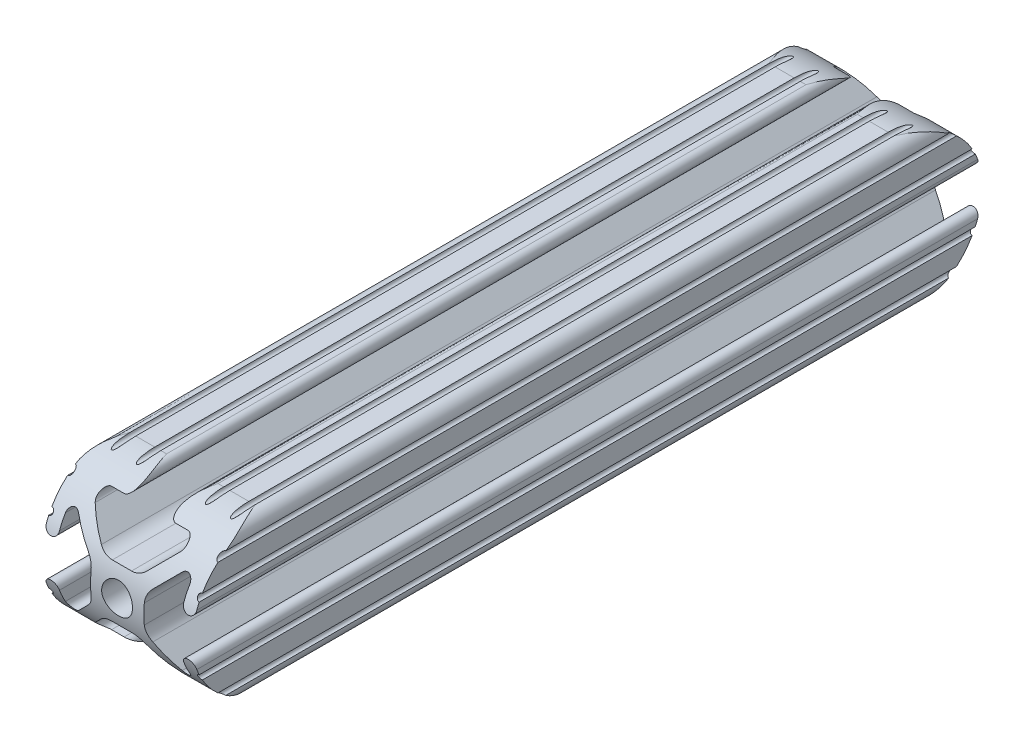
SolidWorks part; units mm, degrees
ref_plane "Front Plane" through (0, 0, 0) normal (0, 0, 1) x (1, 0, 0)
ref_plane "Top Plane" through (0, 0, 0) normal (0, 1, 0) x (1, 0, 0)
ref_plane "Right Plane" through (0, 0, 0) normal (1, 0, 0) x (0, 0, -1)
ref_plane "Plane1" through (0, 0, -450.85) normal (0, 0, -1) x (-1, 0, 0)
sketch "Sketch1" plane through (0, 0, -450.85) normal (0, 0, -1) x (-1, 0, 0)
  line L0 (12.7, -9.5504) -> (12.7, -6.3331)
  line L1 (12.7, -5.3171) -> (12.7, -4.3434)
  line L2 (10.4902, -4.3434) -> (10.4902, -6.4748)
  line L3 (8.7558, -7.1932) -> (5.4257, -3.8632)
  line L4 (4.4958, -1.6181) -> (4.4958, 1.6181)
  line L5 (5.4257, 3.8632) -> (8.7558, 7.1932)
  line L6 (10.4902, 6.4748) -> (10.4902, 4.3434)
  line L7 (12.7, 4.3434) -> (12.7, 5.3171)
  line L8 (12.7, 6.3331) -> (12.7, 9.5504)
  line L9 (9.5504, 12.7) -> (6.3331, 12.7)
  line L10 (5.3171, 12.7) -> (4.3434, 12.7)
  line L11 (4.3434, 10.4902) -> (6.4748, 10.4902)
  line L12 (7.1932, 8.7558) -> (3.8632, 5.4257)
  line L13 (1.6181, 4.4958) -> (-1.6181, 4.4958)
  line L14 (-3.8632, 5.4257) -> (-7.1932, 8.7558)
  line L15 (-6.4748, 10.4902) -> (-4.3434, 10.4902)
  line L16 (-4.3434, 12.7) -> (-5.3171, 12.7)
  line L17 (-6.3331, 12.7) -> (-9.5504, 12.7)
  line L18 (-12.7, 9.5504) -> (-12.7, 6.3331)
  line L19 (-12.7, 5.3171) -> (-12.7, 4.3434)
  line L20 (-10.4902, 4.3434) -> (-10.4902, 6.4748)
  line L21 (-8.7558, 7.1932) -> (-5.4257, 3.8632)
  line L22 (-4.4958, 1.6181) -> (-4.4958, -1.6181)
  line L23 (-5.4257, -3.8632) -> (-8.7558, -7.1932)
  line L24 (-10.4902, -6.4748) -> (-10.4902, -4.3434)
  line L25 (-12.7, -4.3434) -> (-12.7, -5.3171)
  line L26 (-12.7, -6.3331) -> (-12.7, -9.5504)
  line L27 (-9.5504, -12.7) -> (-6.3331, -12.7)
  line L28 (-5.3171, -12.7) -> (-4.3434, -12.7)
  line L29 (-4.3434, -10.4902) -> (-6.4748, -10.4902)
  line L30 (-7.1932, -8.7558) -> (-3.8632, -5.4257)
  line L31 (-1.6181, -4.4958) -> (1.6181, -4.4958)
  line L32 (3.8632, -5.4257) -> (7.1932, -8.7558)
  line L33 (6.4748, -10.4902) -> (4.3434, -10.4902)
  line L34 (4.3434, -12.7) -> (5.3171, -12.7)
  line L35 (6.3331, -12.7) -> (9.5504, -12.7)
  arc A0 (12.6998, -10.5664) -> (12.7, -9.5504) centre (12.7, -10.0584) cw
  arc A1 (12.7, -6.3331) -> (12.7, -5.3171) centre (12.7, -5.8251) cw
  arc A2 (12.7, -4.3434) -> (10.4902, -4.3434) centre (11.5951, -4.3434) ccw
  arc A3 (10.4902, -6.4748) -> (8.7558, -7.1932) centre (9.4742, -6.4748) cw
  arc A4 (5.4257, -3.8632) -> (4.4958, -1.6181) centre (7.6708, -1.6181) cw
  arc A5 (4.4958, 1.6181) -> (5.4257, 3.8632) centre (7.6708, 1.6181) cw
  arc A6 (8.7558, 7.1932) -> (10.4902, 6.4748) centre (9.4742, 6.4748) cw
  arc A7 (10.4902, 4.3434) -> (12.7, 4.3434) centre (11.5951, 4.3434) ccw
  arc A8 (12.7, 5.3171) -> (12.7, 6.3331) centre (12.7, 5.8251) cw
  arc A9 (12.7, 9.5504) -> (12.6998, 10.5664) centre (12.7, 10.0584) cw
  arc A10 (12.6998, 10.5664) -> (10.5664, 12.6998) centre (10.5918, 10.5918) ccw
  arc A11 (10.5664, 12.6998) -> (9.5504, 12.7) centre (10.0584, 12.7) cw
  arc A12 (6.3331, 12.7) -> (5.3171, 12.7) centre (5.8251, 12.7) cw
  arc A13 (4.3434, 12.7) -> (4.3434, 10.4902) centre (4.3434, 11.5951) ccw
  arc A14 (6.4748, 10.4902) -> (7.1932, 8.7558) centre (6.4748, 9.4742) cw
  arc A15 (3.8632, 5.4257) -> (1.6181, 4.4958) centre (1.6181, 7.6708) cw
  arc A16 (-1.6181, 4.4958) -> (-3.8632, 5.4257) centre (-1.6181, 7.6708) cw
  arc A17 (-7.1932, 8.7558) -> (-6.4748, 10.4902) centre (-6.4748, 9.4742) cw
  arc A18 (-4.3434, 10.4902) -> (-4.3434, 12.7) centre (-4.3434, 11.5951) ccw
  arc A19 (-5.3171, 12.7) -> (-6.3331, 12.7) centre (-5.8251, 12.7) cw
  arc A20 (-9.5504, 12.7) -> (-10.5664, 12.6998) centre (-10.0584, 12.7) cw
  arc A21 (-10.5664, 12.6998) -> (-12.6998, 10.5664) centre (-10.5918, 10.5918) ccw
  arc A22 (-12.6998, 10.5664) -> (-12.7, 9.5504) centre (-12.7, 10.0584) cw
  arc A23 (-12.7, 6.3331) -> (-12.7, 5.3171) centre (-12.7, 5.8251) cw
  arc A24 (-12.7, 4.3434) -> (-10.4902, 4.3434) centre (-11.5951, 4.3434) ccw
  arc A25 (-10.4902, 6.4748) -> (-8.7558, 7.1932) centre (-9.4742, 6.4748) cw
  arc A26 (-5.4257, 3.8632) -> (-4.4958, 1.6181) centre (-7.6708, 1.6181) cw
  arc A27 (-4.4958, -1.6181) -> (-5.4257, -3.8632) centre (-7.6708, -1.6181) cw
  arc A28 (-8.7558, -7.1932) -> (-10.4902, -6.4748) centre (-9.4742, -6.4748) cw
  arc A29 (-10.4902, -4.3434) -> (-12.7, -4.3434) centre (-11.5951, -4.3434) ccw
  arc A30 (-12.7, -5.3171) -> (-12.7, -6.3331) centre (-12.7, -5.8251) cw
  arc A31 (-12.7, -9.5504) -> (-12.6998, -10.5664) centre (-12.7, -10.0584) cw
  arc A32 (-12.6998, -10.5664) -> (-10.5664, -12.6998) centre (-10.5918, -10.5918) ccw
  arc A33 (-10.5664, -12.6998) -> (-9.5504, -12.7) centre (-10.0584, -12.7) cw
  arc A34 (-6.3331, -12.7) -> (-5.3171, -12.7) centre (-5.8251, -12.7) cw
  arc A35 (-4.3434, -12.7) -> (-4.3434, -10.4902) centre (-4.3434, -11.5951) ccw
  arc A36 (-6.4748, -10.4902) -> (-7.1932, -8.7558) centre (-6.4748, -9.4742) cw
  arc A37 (-3.8632, -5.4257) -> (-1.6181, -4.4958) centre (-1.6181, -7.6708) cw
  arc A38 (1.6181, -4.4958) -> (3.8632, -5.4257) centre (1.6181, -7.6708) cw
  arc A39 (7.1932, -8.7558) -> (6.4748, -10.4902) centre (6.4748, -9.4742) cw
  arc A40 (4.3434, -10.4902) -> (4.3434, -12.7) centre (4.3434, -11.5951) ccw
  arc A41 (5.3171, -12.7) -> (6.3331, -12.7) centre (5.8251, -12.7) cw
  arc A42 (9.5504, -12.7) -> (10.5664, -12.6998) centre (10.0584, -12.7) cw
  arc A43 (10.5664, -12.6998) -> (12.6998, -10.5664) centre (10.5918, -10.5918) ccw
  circle A44 centre (0, 0) radius 2.6035
extrude "Boss-Extrude1" add sketch "Sketch1" against normal blind 133.35
ref_plane "Plane2" through (-12.7, -9.5504, -450.85) normal (0, 0, -1) x (-1, 0, 0)
sketch "Sketch3" plane through (-12.7, 0, 0) normal (-1, 0, 0) x (0, 0, 1)
  line L0 (-450.85, -1.6181) -> (-450.85, 1.6181) construction
  line L1 (-317.5, -12.6998) -> (-450.85, -12.6998) construction
  line L2 (-317.5, 12.6998) -> (-450.85, 12.6998) construction
  line L3 (-438.1502, -12.6998) -> (-438.1502, -16.2662)
  line L4 (-438.1502, -16.2662) -> (-454.3878, -16.2662)
  line L5 (-454.3878, -16.2662) -> (-454.3878, 14.9464)
  line L6 (-454.3878, 14.9464) -> (-438.1502, 14.9464)
  line L7 (-438.1502, 14.9464) -> (-438.1502, 12.6998)
  line L8 (-317.5, 6.3331) -> (-317.5, 9.5504) construction
  line L9 (-317.5, 12.7) -> (-450.85, 12.7) construction
  line L10 (-317.5, -12.7) -> (-450.85, -12.7) construction
  line L11 (-330.2, -12.7) -> (-330.2, -16.2662)
  line L12 (-330.2, -16.2662) -> (-176.4556, -16.2662)
  line L13 (-176.4556, -16.2662) -> (-176.4556, 14.9464)
  line L14 (-176.4556, 14.9464) -> (-330.2, 14.9464)
  line L15 (-330.2, 14.9464) -> (-330.2, 12.7)
  arc A0 (-438.1502, 12.6998) -> (-438.1502, -12.6998) centre (-438.1502, 0) ccw
  arc A1 (-330.2, -12.7) -> (-330.2, 12.7) centre (-330.2, 0) ccw
extrude "Cut-Extrude1" cut sketch "Sketch3" against normal through all
ref_plane "Plane3" through (0, 0, -317.5) normal (0, 0, 1) x (1, 0, 0)
